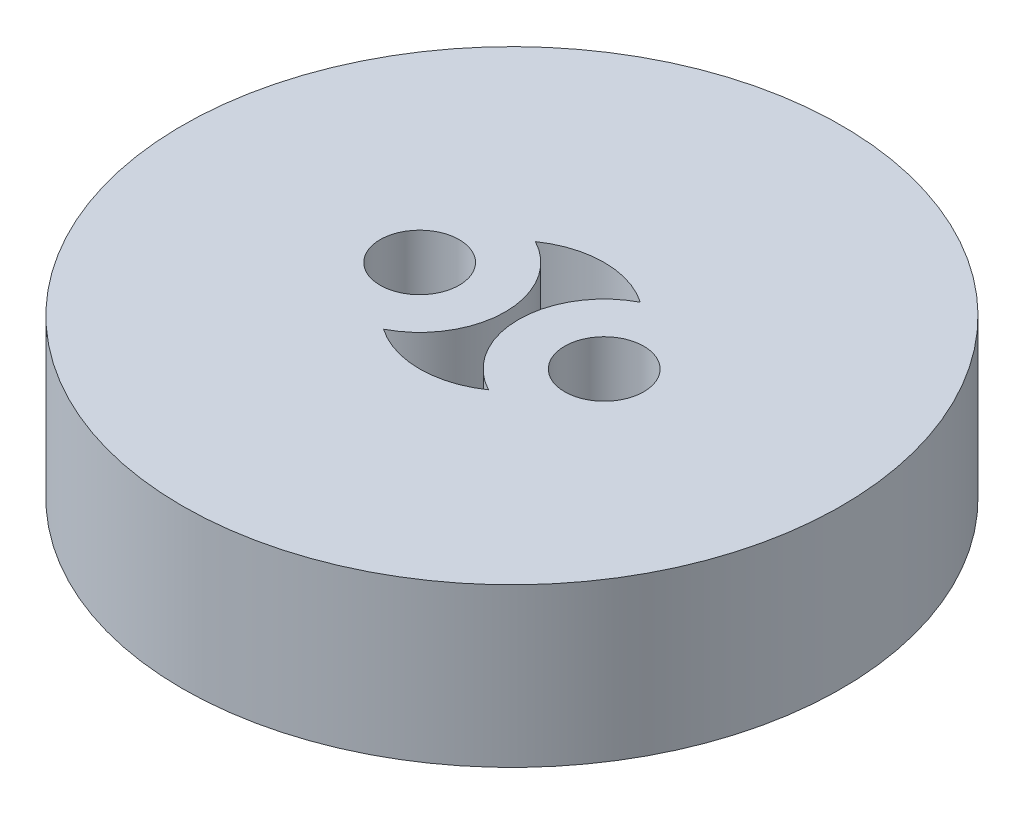
SolidWorks part; units mm, degrees
ref_plane "Plan de face" through (0, 0, 0) normal (0, 0, 1) x (1, 0, 0)
ref_plane "Plan de dessus" through (0, 0, 0) normal (0, 1, 0) x (1, 0, 0)
ref_plane "Plan de droite" through (0, 0, 0) normal (1, 0, 0) x (0, 0, -1)
sketch "Esquisse1" plane through (0, 0, 0) normal (0, 1, 0) x (1, 0, 0)
  line L0 (-3.5, 0) -> (3.5, 0) construction
  circle A0 centre (0, 0) radius 12.5
  circle A2 centre (-3.5, 0) radius 1.5
  circle A3 centre (3.5, 0) radius 1.5
  arc A4 (1.9911, 2.8785) -> (1.9911, -2.8785) centre (3.5, 0) ccw
  arc A5 (-1.9911, -2.8785) -> (-1.9911, 2.8785) centre (-3.5, 0) ccw
  arc A6 (-1.9911, -2.8785) -> (1.9911, -2.8785) centre (0, 0) ccw
  arc A9 (1.9911, 2.8785) -> (-1.9911, 2.8785) centre (0, 0) ccw
  circle A10 centre (-3.5, 0) radius 3.25 construction
  circle A11 centre (3.5, 0) radius 3.25 construction
  dimension "D1" = 25
  dimension "D2" = 6.5
  dimension "D3" = 6.5
  dimension "D4" = 7
  dimension "D5" = 3
  dimension "D6" = 3
  dimension "D7" = 3.5
  dimension "D8" = 3.5
  dimension "D9" = 3.25
  dimension "D10" = 3.25
  dimension "D11" = 3.5
extrude "Boss.-Extru.1" add sketch "Esquisse1" along normal blind 6
